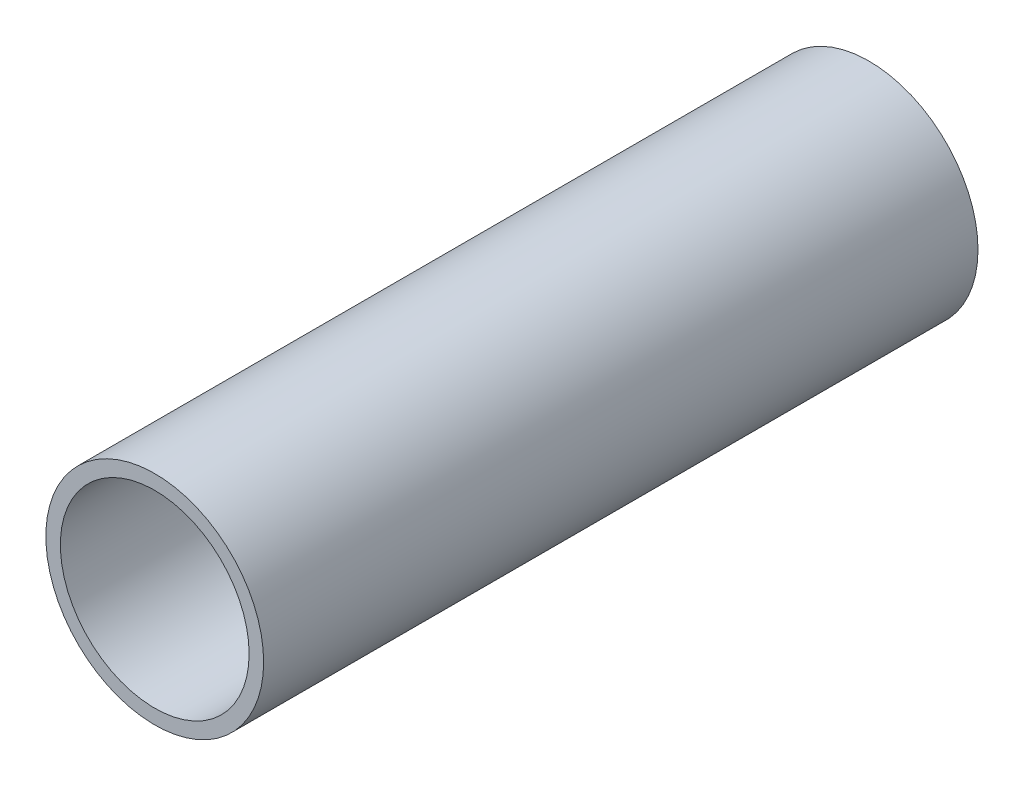
SolidWorks part; units mm, degrees
ref_plane "Front Plane" through (0, 0, 0) normal (0, 0, 1) x (1, 0, 0)
ref_plane "Top Plane" through (0, 0, 0) normal (0, 1, 0) x (1, 0, 0)
ref_plane "Right Plane" through (0, 0, 0) normal (1, 0, 0) x (0, 0, -1)
sketch "Sketch1" plane through (0, 0, 0) normal (0, 0, 1) x (1, 0, 0)
  circle A0 centre (0, 0) radius 9.525
  circle A1 centre (0, 0) radius 8.255
  dimension "D1" = 16.51
  dimension "D2" = 19.05
extrude "Boss-Extrude1" add sketch "Sketch1" along normal blind 62.484
